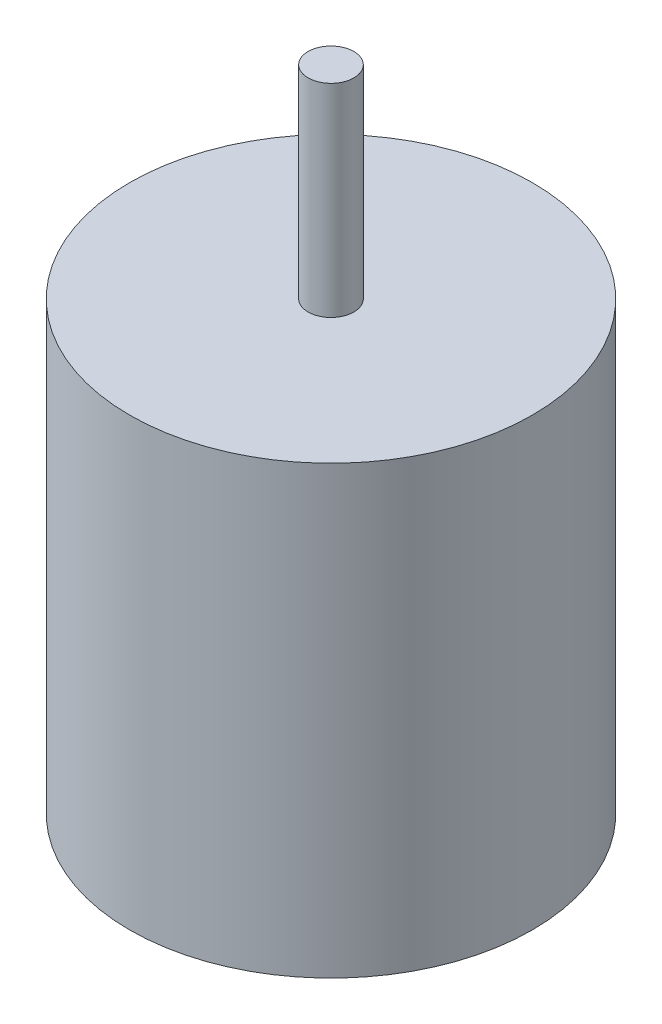
SolidWorks part; units mm, degrees
ref_plane "Front Plane" through (0, 0, 0) normal (0, 0, 1) x (1, 0, 0)
ref_plane "Top Plane" through (0, 0, 0) normal (0, 1, 0) x (1, 0, 0)
ref_plane "Right Plane" through (0, 0, 0) normal (1, 0, 0) x (0, 0, -1)
sketch "Sketch1" plane through (0, 0, 0) normal (0, 1, 0) x (1, 0, 0)
  circle A0 centre (0, 0) radius 14
  dimension "D1" = 28
extrude "Boss-Extrude1" add sketch "Sketch1" along normal blind 31
sketch "Sketch2" plane through (0, 31, 0) normal (0, 1, 0) x (1, 0, 0)
  circle A0 centre (0, 0) radius 1.59
  dimension "D1" = 3.18
extrude "Boss-Extrude2" add sketch "Sketch2" along normal blind 45.1 from surface at -31 starting at face at (0, 0, 14)
